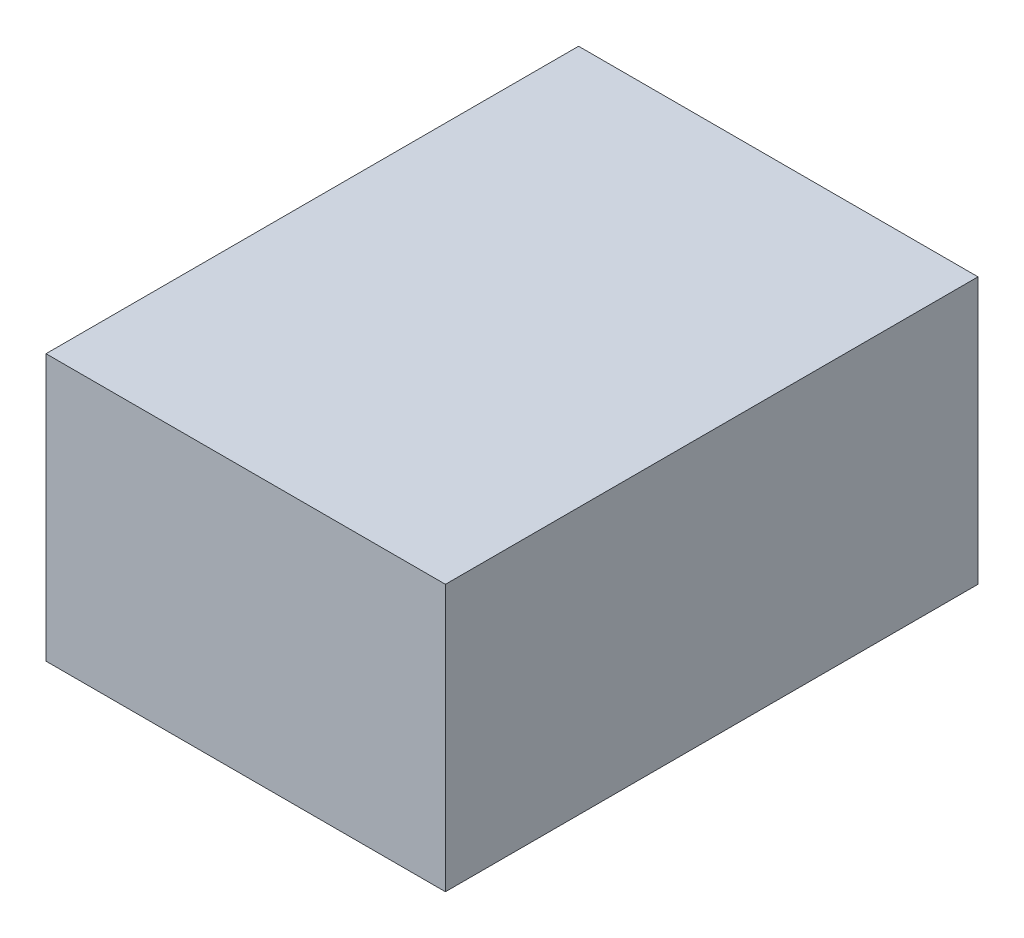
SolidWorks part; units mm, degrees
ref_plane "Front Plane" through (0, 0, 0) normal (0, 0, 1) x (1, 0, 0)
ref_plane "Top Plane" through (0, 0, 0) normal (0, 1, 0) x (1, 0, 0)
ref_plane "Right Plane" through (0, 0, 0) normal (1, 0, 0) x (0, 0, -1)
sketch "Sketch1" plane through (0, 0, 0) normal (0, 0, 1) x (1, 0, 0)
  line L1 (-3, -2) -> (3, -2)
  line L2 (-3, -2) -> (-3, 2)
  line L3 (-3, 2) -> (3, 2)
  line L4 (3, -2) -> (3, 2)
  line L5 (-3, -2) -> (3, 2) construction
  line L6 (-3, 2) -> (3, -2) construction
  point P0 (0, 0)
  dimension "D1" = 6
  dimension "D2" = 4
extrude "Boss-Extrude1" add sketch "Sketch1" along normal blind 8
